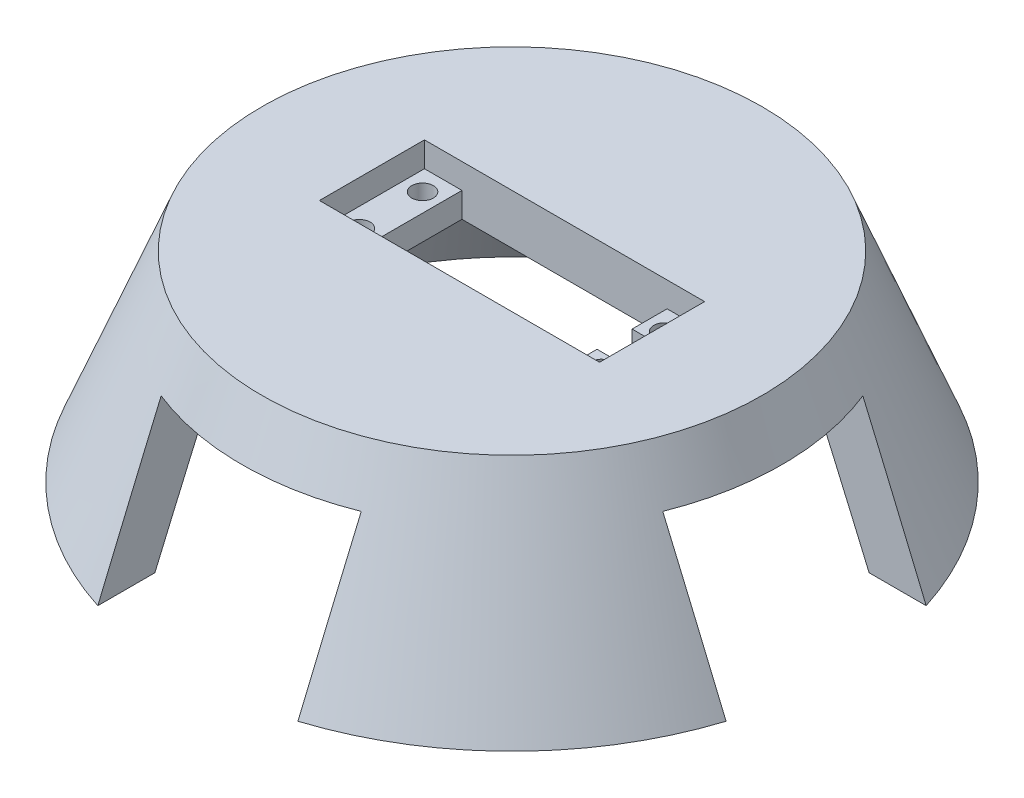
SolidWorks part; units mm, degrees
ref_plane "Front Plane" through (0, 0, 0) normal (0, 0, 1) x (1, 0, 0)
ref_plane "Top Plane" through (0, 0, 0) normal (0, 1, 0) x (1, 0, 0)
ref_plane "Right Plane" through (0, 0, 0) normal (1, 0, 0) x (0, 0, -1)
sketch "Sketch2" plane through (0, 0, 0) normal (0, 0, 1) x (1, 0, 0)
  line L0 (0, 0) -> (0, 40)
  line L1 (0, 40) -> (-50, 40)
  line L2 (-50, 40) -> (-65.8963, 0)
  line L3 (-65.8963, 0) -> (0, 0)
  point P3 (-65.8963, 0)
  point P6 (0, 0)
  point P7 (0, 0)
  point P8 (0, 50)
  dimension "D3" = 40
revolve "Revolve1" add sketch "Sketch2" angle 360 about L0
shell "Shell1" thickness 10
sketch "Sketch4" plane through (0, 40, 0) normal (0, 1, 0) x (1, 0, 0)
  line L0 (0, -10.5) -> (0, 0) construction
  line L1 (-20.5, -10.5) -> (20.5, -10.5)
  line L2 (-20.5, -10.5) -> (-20.5, 10.5)
  line L3 (-20.5, 10.5) -> (20.5, 10.5)
  line L4 (20.5, -10.5) -> (20.5, 10.5)
  line L5 (0, 0) -> (-20.5, 0) construction
  dimension "D1" = 41
  dimension "D2" = 21
  dimension "D3" = 10.5
extrude "Cut-Extrude1" cut sketch "Sketch4" against normal blind 10
sketch "Sketch5" plane through (0, 40, 0) normal (0, 1, 0) x (1, 0, 0)
  line L1 (-20.5, -10.5) -> (-28, -10.5)
  line L2 (-20.5, -10.5) -> (-20.5, 10.5)
  line L3 (-20.5, 10.5) -> (-28, 10.5)
  line L4 (-28, -10.5) -> (-28, 10.5)
  dimension "D1" = 7.5
  dimension "D2" = 21
extrude "Cut-Extrude2" cut sketch "Sketch5" against normal blind 5
sketch "Sketch6" plane through (0, 35, 0) normal (0, 1, 0) x (1, 0, 0)
  line L0 (-28, 10.5) -> (-24.19, 10.5) construction
  line L1 (-20.5, 10.5) -> (-28, 10.5) construction
  line L2 (-24.19, 10.5) -> (-24.19, 6.31) construction
  circle A0 centre (-24.19, 6.31) radius 2.16
  dimension "D3" = 4.32
  dimension "D1" = 4.19
  dimension "D2" = 3.81
extrude "Cut-Extrude3" cut sketch "Sketch6" against normal blind 5
mirror "Mirror2" about plane through (0, 0, 0) normal (0, 0, 1) of "Cut-Extrude3"
mirror "Mirror1" about plane through (0, 0, 0) normal (1, 0, 0) of "Mirror2", "Cut-Extrude3", "Cut-Extrude2"
sketch "Sketch7" plane through (0, 35, 0) normal (0, 1, 0) x (1, 0, 0)
  line L0 (20.5, -10.5) -> (20.5, 10.5) construction
  line L1 (20.5, 0) -> (24.5, 0)
  line L2 (20.5, 0) -> (20.5, -3.5)
  line L3 (20.5, -3.5) -> (24.5, -3.5)
  line L4 (24.5, 0) -> (24.5, -3.5)
  dimension "D1" = 3.5
  dimension "D2" = 4
extrude "Cut-Extrude4" cut sketch "Sketch7" against normal blind 10
mirror "Mirror3" about plane through (0, 0, 0) normal (0, 0, 1) of "Cut-Extrude4"
sketch "Sketch8" plane through (0, 0, 0) normal (0, -1, 0) x (1, 0, 0)
  line L1 (-20, -75) -> (20, -75)
  line L2 (-20, -75) -> (-20, 75)
  line L3 (-20, 75) -> (20, 75)
  line L4 (20, -75) -> (20, 75)
  line L5 (-20, -75) -> (20, 75) construction
  line L6 (-20, 75) -> (20, -75) construction
  line L7 (-75, -20) -> (75, -20)
  line L8 (-75, -20) -> (-75, 20)
  line L9 (-75, 20) -> (75, 20)
  line L10 (75, -20) -> (75, 20)
  line L11 (-75, -20) -> (75, 20) construction
  line L12 (-75, 20) -> (75, -20) construction
  point P0 (0, 0)
  point P6 (0, 0)
  circle M7 centre (0, 0) radius 55.1356
  circle M8 centre (0, 0) radius 65.8963
  dimension "D1" = 150
  dimension "D2" = 40
  dimension "D3" = 150
  dimension "D4" = 40
extrude "Cut-Extrude7" cut sketch "Sketch8" along direction (0, -1, 0) on the side against the normal up to surface (30 mm away) contours L2 L9 L4 M7 | L4 L2 M7 M8 | L9 L7 L2 M7 | L9 L7 M8 M7 | L4 L2 M8 M7 | L7 L2 L4 M7 | L9 L7 M7 M8 | L9 L4 L7 M7
